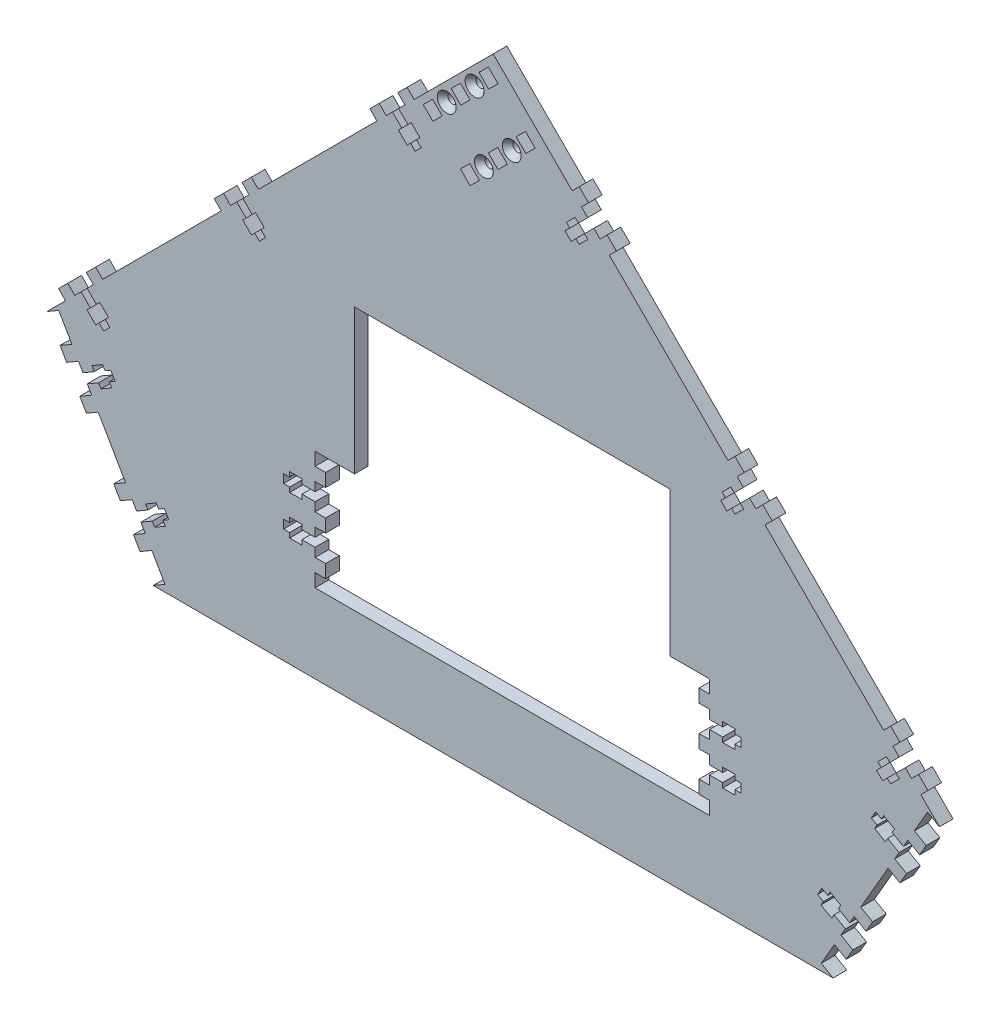
SolidWorks part; units mm, degrees
material "Acrylic (Blue)"
ref_plane "Front Plane" through (0, 0, 0) normal (0, 0, 1) x (1, 0, 0)
ref_plane "Top Plane" through (0, 0, 0) normal (0, 1, 0) x (1, 0, 0)
ref_plane "Right Plane" through (0, 0, 0) normal (1, 0, 0) x (0, 0, -1)
sketch "Sketch1" plane through (0, 0, 0) normal (0, 0, 1) x (1, 0, 0)
  line L0 (0, 0) -> (0, 304.4261) construction
  line L1 (0, 304.4261) -> (215.5261, 88.9)
  line L2 (215.5261, 88.9) -> (164.1997, 0)
  line L3 (164.1997, 0) -> (0, 0)
  line L4 (0, 304.4261) -> (-215.5261, 88.9)
  line L5 (-215.5261, 88.9) -> (-164.1997, 0)
  line L6 (-164.1997, 0) -> (0, 0)
  line L7 (-215.5261, 88.9) -> (215.5261, 88.9) construction
  line L8 (0, 304.4261) -> (3.5921, 308.0182) construction
  line L9 (3.5921, 308.0182) -> (219.1182, 92.4921) construction
  line L10 (219.1182, 92.4921) -> (215.5261, 88.9) construction
  line L11 (3.5921, 308.0182) -> (0, 311.6104) construction
  line L12 (0, 311.6104) -> (-219.1182, 92.4921) construction
  line L13 (-219.1182, 92.4921) -> (-215.5261, 88.9) construction
  line L14 (215.5261, 88.9) -> (219.9256, 86.36) construction
  line L15 (219.9256, 86.36) -> (168.5991, -2.54) construction
  line L16 (168.5991, -2.54) -> (164.1997, 0) construction
  line L17 (164.1997, 0) -> (164.1997, -12.7) construction
  line L18 (164.1997, -12.7) -> (-164.1997, -12.7) construction
  line L19 (-164.1997, -12.7) -> (-164.1997, 0) construction
  line L20 (-164.1997, 0) -> (-168.5991, -2.54) construction
  line L21 (-168.5991, -2.54) -> (-219.9256, 86.36) construction
  line L22 (-219.9256, 86.36) -> (-215.5261, 88.9) construction
  dimension "D1" = 304.8
  dimension "D2" = 120
  dimension "D3" = 88.9
  dimension "D4" = 5.08
  dimension "D5" = 12.7
extrude "Boss-Extrude1" add sketch "Sketch1" along normal blind 6.604
sketch "Sketch2" plane through (0, 0, 6.604) normal (0, 0, 1) x (1, 0, 0)
  line L0 (215.5261, 88.9) -> (0, 304.4261) construction
  line L1 (-66.9554, 165.1) -> (85.4446, 165.1)
  line L2 (-66.9554, 38.1) -> (85.4446, 38.1)
  line L3 (85.4446, 165.1) -> (85.4446, 95.25)
  line L4 (-66.9554, 165.1) -> (-66.9554, 95.25)
  line L6 (-164.1997, 0) -> (164.1997, 0) construction
  line L7 (-66.9554, 38.1) -> (-86.0054, 38.1)
  line L9 (-66.9554, 95.25) -> (-86.0054, 95.25)
  line L10 (-86.0054, 38.1) -> (-86.0054, 95.25)
  line L11 (85.4446, 38.1) -> (104.4946, 38.1)
  line L13 (85.4446, 95.25) -> (104.4946, 95.25)
  line L14 (104.4946, 38.1) -> (104.4946, 95.25)
  dimension "D1" = 127
  dimension "D2" = 38.1
  dimension "D3" = 38.1
  dimension "D4" = 152.4
  dimension "D5" = 19.05
  dimension "D6" = 57.15
extrude "Cut-Extrude1" cut sketch "Sketch2" against normal through all
sketch "Sketch3" plane through (0, 0, 6.604) normal (0, 0, 1) x (1, 0, 0)
  line L0 (-209.8069, 92.202) -> (-215.5261, 88.9)
  line L1 (-215.5261, 88.9) -> (-164.1997, 0)
  line L2 (-164.1997, 0) -> (-158.4805, 3.302)
  line L3 (-158.4805, 3.302) -> (-209.8069, 92.202)
  line L4 (0, 304.4261) -> (0, 0) construction
  line L5 (158.4805, 3.302) -> (209.8069, 92.202)
  line L6 (164.1997, 0) -> (158.4805, 3.302)
  line L7 (215.5261, 88.9) -> (164.1997, 0)
  line L8 (209.8069, 92.202) -> (215.5261, 88.9)
  dimension "D1" = 6.604
extrude "Cut-Extrude2" cut sketch "Sketch3" against normal through all
sketch "Sketch8" plane through (0, 0, 6.604) normal (0, 0, 1) x (1, 0, 0)
  line L0 (0, 304.4261) -> (-215.5261, 88.9) construction
  line L1 (215.5261, 88.9) -> (0, 304.4261) construction
  line B0 (-20.2954, 279.8202) -> (-15.8053, 284.3104)
  line B1 (-15.8053, 284.3104) -> (-11.1355, 279.6406)
  line B2 (-11.1355, 279.6406) -> (-15.6256, 275.1505)
  line B3 (-15.6256, 275.1505) -> (-20.2954, 279.8202)
  line B4 (-33.7658, 266.3499) -> (-29.2756, 270.84)
  line B5 (-29.2756, 270.84) -> (-24.6059, 266.1703)
  line B6 (-24.6059, 266.1703) -> (-29.096, 261.6801)
  line B7 (-29.096, 261.6801) -> (-33.7658, 266.3499)
  circle B8 centre (-22.4506, 272.9953) radius 2.1526
  line B9 (-6.825, 293.2906) -> (-2.3349, 297.7808)
  line B10 (-2.3349, 297.7808) -> (2.3349, 293.111)
  line B11 (-2.1553, 288.6209) -> (2.3349, 293.111)
  line B12 (-6.825, 293.2906) -> (-2.1553, 288.6209)
  circle B13 centre (-8.9803, 286.4656) radius 2.1527
  line B14 (-2.3349, 261.8597) -> (2.1553, 266.3499)
  line B15 (2.1553, 266.3499) -> (6.825, 261.6801)
  line B16 (6.825, 261.6801) -> (2.3349, 257.19)
  line B17 (2.3349, 257.19) -> (-2.3349, 261.8597)
  line B18 (-15.8053, 248.3893) -> (-11.3151, 252.8795)
  line B19 (-11.3151, 252.8795) -> (-6.6454, 248.2097)
  line B20 (-6.6454, 248.2097) -> (-11.1355, 243.7196)
  line B21 (-11.1355, 243.7196) -> (-15.8053, 248.3893)
  circle B22 centre (-4.4901, 255.0347) radius 2.1526
  line B23 (11.1355, 275.3301) -> (15.6256, 279.8202)
  line B24 (15.6256, 279.8202) -> (20.2954, 275.1505)
  line B25 (15.8053, 270.6604) -> (20.2954, 275.1505)
  line B26 (11.1355, 275.3301) -> (15.8053, 270.6604)
  circle B27 centre (8.9803, 268.5051) radius 2.1527
  dimension "D1" = 6.35
  dimension "D2" = 25.4
  dimension "D3" = 6.35
sketch_block_instance "BOLT_HOLE_2X-1"
sketch_block "BOLT_HOLE_2X" parameters "D1"=4.3053, "D2"=6.35, "D3"=6.35, "D4"=6.604
sketch_block_instance "BOLT_HOLE_2X-2"
extrude "Cut-Extrude4" cut sketch "Sketch8" against normal through all
sketch "Sketch4" plane through (0, 0, 6.604) normal (0, 0, 1) x (1, 0, 0)
  line L0 (0, 304.4261) -> (-215.5261, 88.9) construction
  line L1 (-59.5391, 251.712) -> (-116.7882, 194.4629) construction
  line L3 (-134.7487, 176.5024) -> (-191.9979, 119.2533) construction
  line L4 (215.5261, 88.9) -> (0, 304.4261) construction
  line L5 (134.7487, 176.5024) -> (191.9979, 119.2533) construction
  line L6 (59.5391, 251.712) -> (116.7882, 194.4629) construction
  line L7 (215.5261, 88.9) -> (209.8069, 92.202) construction
  line L8 (-158.4805, 3.302) -> (-209.8069, 92.202) construction
  line L9 (-209.8069, 92.202) -> (-215.5261, 88.9) construction
  line L11 (158.4805, 3.302) -> (164.1997, 0) construction
  line L13 (-164.1997, 0) -> (-158.4805, 3.302) construction
  line L14 (209.8069, 92.202) -> (158.4805, 3.302) construction
  line L15 (104.4946, 38.1) -> (104.4946, 95.25) construction
  line L16 (104.4946, 95.25) -> (85.4446, 95.25) construction
  line L17 (-86.0054, 95.25) -> (-86.0054, 38.1) construction
  line B0 (-48.6191, 255.807) -> (-44.129, 251.3169) construction
  line B1 (-44.129, 251.3169) -> (-45.7454, 249.7005) construction
  line B2 (-45.7454, 249.7005) -> (-41.5427, 245.4977) construction
  line B3 (-41.5427, 245.4977) -> (-39.9262, 247.1142) construction
  line B4 (-39.9262, 247.1142) -> (-37.6632, 244.8511) construction
  line B5 (-37.6632, 244.8511) -> (-34.7177, 247.7967) construction
  line B6 (-34.7177, 247.7967) -> (-36.9807, 250.0597) construction
  line B7 (-36.9807, 250.0597) -> (-35.3642, 251.6761) construction
  line B8 (-35.3642, 251.6761) -> (-39.567, 255.8789) construction
  line B9 (-39.567, 255.8789) -> (-41.1835, 254.2624) construction
  line B10 (-41.1835, 254.2624) -> (-45.6736, 258.7526) construction
  line B11 (-42.6562, 261.7699) -> (-46.0687, 265.1824) construction
  line B12 (-46.0687, 265.1824) -> (-41.5786, 269.6726) construction
  line B13 (-41.5786, 269.6726) -> (-38.1661, 266.2601) construction
  line B14 (-48.6191, 255.807) -> (-51.6365, 252.7897) construction
  line B15 (-51.6365, 252.7897) -> (-55.049, 256.2022) construction
  line B16 (-55.049, 256.2022) -> (-59.5391, 251.712) construction
  line B17 (-59.5391, 251.712) -> (-56.1266, 248.2995) construction
  line B18 (-45.6736, 258.7526) -> (-48.6191, 255.807) construction
  line B19 (-123.8288, 180.5974) -> (-119.3386, 176.1073) construction
  line B20 (-119.3386, 176.1073) -> (-120.9551, 174.4908) construction
  line B21 (-120.9551, 174.4908) -> (-116.7523, 170.2881) construction
  line B22 (-116.7523, 170.2881) -> (-115.1359, 171.9045) construction
  line B23 (-115.1359, 171.9045) -> (-112.8728, 169.6415) construction
  line B24 (-112.8728, 169.6415) -> (-109.9273, 172.587) construction
  line B25 (-109.9273, 172.587) -> (-112.1903, 174.85) construction
  line B26 (-112.1903, 174.85) -> (-110.5739, 176.4665) construction
  line B27 (-110.5739, 176.4665) -> (-114.7767, 180.6692) construction
  line B28 (-114.7767, 180.6692) -> (-116.3931, 179.0528) construction
  line B29 (-116.3931, 179.0528) -> (-120.8832, 183.5429) construction
  line B30 (-117.8659, 186.5603) -> (-121.2784, 189.9728) construction
  line B31 (-121.2784, 189.9728) -> (-116.7882, 194.4629) construction
  line B32 (-116.7882, 194.4629) -> (-113.3757, 191.0504) construction
  line B33 (-126.8461, 177.58) -> (-130.2586, 180.9925) construction
  line B34 (-130.2586, 180.9925) -> (-134.7487, 176.5024) construction
  line B35 (-134.7487, 176.5024) -> (-131.3362, 173.0899) construction
  line B36 (-120.8832, 183.5429) -> (-123.8288, 180.5974) construction
  line B37 (-199.0384, 105.3878) -> (-194.5483, 100.8976) construction
  line B38 (-194.5483, 100.8976) -> (-196.1647, 99.2812) construction
  line B39 (-196.1647, 99.2812) -> (-191.962, 95.0784) construction
  line B40 (-191.962, 95.0784) -> (-190.3455, 96.6949) construction
  line B41 (-190.3455, 96.6949) -> (-188.0825, 94.4318) construction
  line B42 (-188.0825, 94.4318) -> (-185.137, 97.3774) construction
  line B43 (-185.137, 97.3774) -> (-187.4, 99.6404) construction
  line B44 (-187.4, 99.6404) -> (-185.7835, 101.2568) construction
  line B45 (-185.7835, 101.2568) -> (-189.9863, 105.4596) construction
  line B46 (-189.9863, 105.4596) -> (-191.6027, 103.8431) construction
  line B47 (-191.6027, 103.8431) -> (-196.0929, 108.3333) construction
  line B48 (-196.0929, 108.3333) -> (-193.0755, 111.3506) construction
  line B49 (-193.0755, 111.3506) -> (-196.488, 114.7631) construction
  line B50 (-196.488, 114.7631) -> (-191.9979, 119.2533) construction
  line B51 (-191.9979, 119.2533) -> (-188.5854, 115.8408) construction
  line B52 (-199.0384, 105.3878) -> (-202.0558, 102.3704) construction
  line B53 (-202.0558, 102.3704) -> (-205.4683, 105.7829) construction
  line B54 (-205.4683, 105.7829) -> (-209.9584, 101.2928) construction
  line B55 (-209.9584, 101.2928) -> (-206.5459, 97.8803) construction
  line B56 (-196.0929, 108.3333) -> (-199.0384, 105.3878) construction
  line B57 (45.6736, 258.7526) -> (41.1835, 254.2624) construction
  line B58 (41.1835, 254.2624) -> (39.567, 255.8789) construction
  line B59 (39.567, 255.8789) -> (35.3642, 251.6761) construction
  line B60 (35.3642, 251.6761) -> (36.9807, 250.0597) construction
  line B61 (36.9807, 250.0597) -> (34.7177, 247.7967) construction
  line B62 (34.7177, 247.7967) -> (37.6632, 244.8511) construction
  line B63 (37.6632, 244.8511) -> (39.9262, 247.1142) construction
  line B64 (39.9262, 247.1142) -> (41.5427, 245.4977) construction
  line B65 (41.5427, 245.4977) -> (45.7454, 249.7005) construction
  line B66 (45.7454, 249.7005) -> (44.129, 251.3169) construction
  line B67 (44.129, 251.3169) -> (48.6191, 255.807) construction
  line B68 (48.6191, 255.807) -> (51.6365, 252.7897) construction
  line B69 (51.6365, 252.7897) -> (55.049, 256.2022) construction
  line B70 (55.049, 256.2022) -> (59.5391, 251.712) construction
  line B71 (59.5391, 251.712) -> (56.1266, 248.2995) construction
  line B72 (45.6736, 258.7526) -> (42.6562, 261.7699) construction
  line B73 (42.6562, 261.7699) -> (46.0687, 265.1824) construction
  line B74 (46.0687, 265.1824) -> (41.5786, 269.6726) construction
  line B75 (41.5786, 269.6726) -> (38.1661, 266.2601) construction
  line B76 (48.6191, 255.807) -> (45.6736, 258.7526) construction
  line B77 (120.8832, 183.5429) -> (116.3931, 179.0528) construction
  line B78 (116.3931, 179.0528) -> (114.7767, 180.6692) construction
  line B79 (114.7767, 180.6692) -> (110.5739, 176.4665) construction
  line B80 (110.5739, 176.4665) -> (112.1903, 174.85) construction
  line B81 (112.1903, 174.85) -> (109.9273, 172.587) construction
  line B82 (109.9273, 172.587) -> (112.8728, 169.6415) construction
  line B83 (112.8728, 169.6415) -> (115.1359, 171.9045) construction
  line B84 (115.1359, 171.9045) -> (116.7523, 170.2881) construction
  line B85 (116.7523, 170.2881) -> (120.9551, 174.4908) construction
  line B86 (120.9551, 174.4908) -> (119.3386, 176.1073) construction
  line B87 (119.3386, 176.1073) -> (123.8288, 180.5974) construction
  line B88 (123.8288, 180.5974) -> (126.8461, 177.58) construction
  line B89 (126.8461, 177.58) -> (130.2586, 180.9925) construction
  line B90 (130.2586, 180.9925) -> (134.7487, 176.5024) construction
  line B91 (134.7487, 176.5024) -> (131.3362, 173.0899) construction
  line B92 (120.8832, 183.5429) -> (117.8659, 186.5603) construction
  line B93 (117.8659, 186.5603) -> (121.2784, 189.9728) construction
  line B94 (121.2784, 189.9728) -> (116.7882, 194.4629) construction
  line B95 (116.7882, 194.4629) -> (113.3757, 191.0504) construction
  line B96 (123.8288, 180.5974) -> (120.8832, 183.5429) construction
  line B97 (196.0929, 108.3333) -> (191.6027, 103.8431) construction
  line B98 (191.6027, 103.8431) -> (189.9863, 105.4596) construction
  line B99 (189.9863, 105.4596) -> (185.7835, 101.2568) construction
  line B100 (185.7835, 101.2568) -> (187.4, 99.6404) construction
  line B101 (187.4, 99.6404) -> (185.137, 97.3774) construction
  line B102 (185.137, 97.3774) -> (188.0825, 94.4318) construction
  line B103 (188.0825, 94.4318) -> (190.3455, 96.6949) construction
  line B104 (190.3455, 96.6949) -> (191.962, 95.0784) construction
  line B105 (191.962, 95.0784) -> (196.1647, 99.2812) construction
  line B106 (196.1647, 99.2812) -> (194.5483, 100.8976) construction
  line B107 (194.5483, 100.8976) -> (199.0384, 105.3878) construction
  line B108 (199.0384, 105.3878) -> (202.0558, 102.3704) construction
  line B109 (202.0558, 102.3704) -> (205.4683, 105.7829) construction
  line B110 (205.4683, 105.7829) -> (209.9584, 101.2928) construction
  line B111 (209.9584, 101.2928) -> (206.5459, 97.8803) construction
  line B112 (193.0755, 111.3506) -> (196.488, 114.7631) construction
  line B113 (196.488, 114.7631) -> (191.9979, 119.2533) construction
  line B114 (191.9979, 119.2533) -> (188.5854, 115.8408) construction
  line B115 (199.0384, 105.3878) -> (196.0929, 108.3333) construction
  line B116 (198.1483, 72.0087) -> (192.6491, 75.1837) construction
  line B117 (192.6491, 75.1837) -> (193.7921, 77.1634) construction
  line B118 (193.7921, 77.1634) -> (188.6447, 80.1352) construction
  line B119 (188.6447, 80.1352) -> (187.5017, 78.1555) construction
  line B120 (187.5017, 78.1555) -> (184.7301, 79.7557) construction
  line B121 (184.7301, 79.7557) -> (182.6473, 76.1482) construction
  line B122 (182.6473, 76.1482) -> (185.4189, 74.548) construction
  line B123 (185.4189, 74.548) -> (184.2759, 72.5683) construction
  line B124 (184.2759, 72.5683) -> (189.4233, 69.5965) construction
  line B125 (189.4233, 69.5965) -> (190.5663, 71.5762) construction
  line B126 (190.5663, 71.5762) -> (196.0655, 68.4012) construction
  line B127 (196.0655, 68.4012) -> (193.9319, 64.7057) construction
  line B128 (193.9319, 64.7057) -> (198.1114, 62.2927) construction
  line B129 (198.1114, 62.2927) -> (194.9364, 56.7934) construction
  line B130 (194.9364, 56.7934) -> (190.7569, 59.2064) construction
  line B131 (198.1483, 72.0087) -> (200.2819, 75.7042) construction
  line B132 (200.2819, 75.7042) -> (204.4614, 73.2912) construction
  line B133 (204.4614, 73.2912) -> (207.6364, 78.7905) construction
  line B134 (207.6364, 78.7905) -> (203.4569, 81.2035) construction
  line B135 (196.0655, 68.4012) -> (198.1483, 72.0087) construction
  line B136 (172.2219, 27.1028) -> (166.7226, 30.2778) construction
  line B137 (166.7226, 30.2778) -> (167.8656, 32.2575) construction
  line B138 (167.8656, 32.2575) -> (162.7183, 35.2293) construction
  line B139 (162.7183, 35.2293) -> (161.5753, 33.2496) construction
  line B140 (161.5753, 33.2496) -> (158.8037, 34.8498) construction
  line B141 (158.8037, 34.8498) -> (156.7209, 31.2423) construction
  line B142 (156.7209, 31.2423) -> (159.4925, 29.6421) construction
  line B143 (159.4925, 29.6421) -> (158.3495, 27.6624) construction
  line B144 (158.3495, 27.6624) -> (163.4968, 24.6906) construction
  line B145 (163.4968, 24.6906) -> (164.6398, 26.6703) construction
  line B146 (164.6398, 26.6703) -> (170.1391, 23.4953) construction
  line B147 (170.1391, 23.4953) -> (168.0055, 19.7998) construction
  line B148 (168.0055, 19.7998) -> (172.1849, 17.3868) construction
  line B149 (172.1849, 17.3868) -> (169.0099, 11.8875) construction
  line B150 (169.0099, 11.8875) -> (164.8305, 14.3005) construction
  line B151 (172.2219, 27.1028) -> (174.3555, 30.7983) construction
  line B152 (174.3555, 30.7983) -> (178.5349, 28.3853) construction
  line B153 (178.5349, 28.3853) -> (181.7099, 33.8846) construction
  line B154 (181.7099, 33.8846) -> (177.5305, 36.2976) construction
  line B155 (170.1391, 23.4953) -> (172.2219, 27.1028) construction
  line B156 (-170.1391, 23.4953) -> (-164.6398, 26.6703) construction
  line B157 (-164.6398, 26.6703) -> (-163.4968, 24.6906) construction
  line B158 (-163.4968, 24.6906) -> (-158.3495, 27.6624) construction
  line B159 (-158.3495, 27.6624) -> (-159.4925, 29.6421) construction
  line B160 (-159.4925, 29.6421) -> (-156.7209, 31.2423) construction
  line B161 (-156.7209, 31.2423) -> (-158.8037, 34.8498) construction
  line B162 (-158.8037, 34.8498) -> (-161.5753, 33.2496) construction
  line B163 (-161.5753, 33.2496) -> (-162.7183, 35.2293) construction
  line B164 (-162.7183, 35.2293) -> (-167.8656, 32.2575) construction
  line B165 (-167.8656, 32.2575) -> (-166.7226, 30.2778) construction
  line B166 (-166.7226, 30.2778) -> (-172.2219, 27.1028) construction
  line B167 (-172.2219, 27.1028) -> (-174.3555, 30.7983) construction
  line B168 (-174.3555, 30.7983) -> (-178.5349, 28.3853) construction
  line B169 (-178.5349, 28.3853) -> (-181.7099, 33.8846) construction
  line B170 (-181.7099, 33.8846) -> (-177.5305, 36.2976) construction
  line B171 (-168.0055, 19.7998) -> (-172.1849, 17.3868) construction
  line B172 (-172.1849, 17.3868) -> (-169.0099, 11.8875) construction
  line B173 (-169.0099, 11.8875) -> (-164.8305, 14.3005) construction
  line B174 (-172.2219, 27.1028) -> (-170.1391, 23.4953) construction
  line B175 (-196.0655, 68.4012) -> (-190.5663, 71.5762) construction
  line B176 (-190.5663, 71.5762) -> (-189.4233, 69.5965) construction
  line B177 (-189.4233, 69.5965) -> (-184.2759, 72.5683) construction
  line B178 (-184.2759, 72.5683) -> (-185.4189, 74.548) construction
  line B179 (-185.4189, 74.548) -> (-182.6473, 76.1482) construction
  line B180 (-182.6473, 76.1482) -> (-184.7301, 79.7557) construction
  line B181 (-184.7301, 79.7557) -> (-187.5017, 78.1555) construction
  line B182 (-187.5017, 78.1555) -> (-188.6447, 80.1352) construction
  line B183 (-188.6447, 80.1352) -> (-193.7921, 77.1634) construction
  line B184 (-193.7921, 77.1634) -> (-192.6491, 75.1837) construction
  line B185 (-192.6491, 75.1837) -> (-198.1483, 72.0087) construction
  line B186 (-200.2819, 75.7042) -> (-204.4614, 73.2912) construction
  line B187 (-204.4614, 73.2912) -> (-207.6364, 78.7905) construction
  line B188 (-207.6364, 78.7905) -> (-203.4569, 81.2035) construction
  line B189 (-196.0655, 68.4012) -> (-193.9319, 64.7057) construction
  line B190 (-193.9319, 64.7057) -> (-198.1114, 62.2927) construction
  line B191 (-198.1114, 62.2927) -> (-194.9364, 56.7934) construction
  line B192 (-194.9364, 56.7934) -> (-190.7569, 59.2064) construction
  line B193 (-198.1483, 72.0087) -> (-196.0655, 68.4012) construction
  line B194 (-86.0054, 78.2828) -> (-92.3554, 78.2828)
  line B195 (-92.3554, 78.2828) -> (-92.3554, 80.5688)
  line B196 (-92.3554, 80.5688) -> (-98.299, 80.5688)
  line B197 (-98.299, 80.5688) -> (-98.299, 78.2828)
  line B198 (-98.299, 78.2828) -> (-101.2454, 78.2828)
  line B199 (-101.2454, 78.2828) -> (-101.2454, 74.1172)
  line B200 (-101.2454, 74.1172) -> (-98.299, 74.1172)
  line B201 (-98.299, 74.1172) -> (-98.299, 71.8312)
  line B202 (-98.299, 71.8312) -> (-92.3554, 71.8312)
  line B203 (-92.3554, 71.8312) -> (-92.3554, 74.1172)
  line B204 (-92.3554, 74.1172) -> (-86.0054, 74.1172)
  line B205 (-86.0054, 69.85) -> (-80.9254, 69.85)
  line B206 (-80.9254, 69.85) -> (-80.9254, 63.5)
  line B207 (-80.9254, 63.5) -> (-86.0054, 63.5)
  line B208 (-86.0054, 78.2828) -> (-86.0054, 82.55)
  line B209 (-86.0054, 82.55) -> (-80.9254, 82.55)
  line B210 (-80.9254, 82.55) -> (-80.9254, 88.9)
  line B211 (-80.9254, 88.9) -> (-86.0054, 88.9)
  line B212 (-86.0054, 74.1172) -> (-86.0054, 78.2828) construction
  line B213 (-80.9254, 44.45) -> (-86.0054, 44.45)
  line B214 (-86.0054, 59.2328) -> (-92.3554, 59.2328)
  line B215 (-92.3554, 59.2328) -> (-92.3554, 61.5188)
  line B216 (-92.3554, 61.5188) -> (-98.299, 61.5188)
  line B217 (-98.299, 61.5188) -> (-98.299, 59.2328)
  line B218 (-98.299, 59.2328) -> (-101.2454, 59.2328)
  line B219 (-101.2454, 59.2328) -> (-101.2454, 55.0672)
  line B220 (-101.2454, 55.0672) -> (-98.299, 55.0672)
  line B221 (-98.299, 55.0672) -> (-98.299, 52.7812)
  line B222 (-98.299, 52.7812) -> (-92.3554, 52.7812)
  line B223 (-92.3554, 52.7812) -> (-92.3554, 55.0672)
  line B224 (-92.3554, 55.0672) -> (-86.0054, 55.0672)
  line B225 (-86.0054, 55.0672) -> (-86.0054, 50.8)
  line B226 (-86.0054, 50.8) -> (-80.9254, 50.8)
  line B227 (-80.9254, 50.8) -> (-80.9254, 44.45)
  line B228 (-86.0054, 59.2328) -> (-86.0054, 63.5)
  line B229 (-86.0054, 55.0672) -> (-86.0054, 59.2328) construction
  line B230 (104.4946, 55.0672) -> (110.8446, 55.0672)
  line B231 (110.8446, 55.0672) -> (110.8446, 52.7812)
  line B232 (110.8446, 52.7812) -> (116.7882, 52.7812)
  line B233 (116.7882, 52.7812) -> (116.7882, 55.0672)
  line B234 (116.7882, 55.0672) -> (119.7346, 55.0672)
  line B235 (119.7346, 55.0672) -> (119.7346, 59.2328)
  line B236 (119.7346, 59.2328) -> (116.7882, 59.2328)
  line B237 (116.7882, 59.2328) -> (116.7882, 61.5188)
  line B238 (116.7882, 61.5188) -> (110.8446, 61.5188)
  line B239 (110.8446, 61.5188) -> (110.8446, 59.2328)
  line B240 (110.8446, 59.2328) -> (104.4946, 59.2328)
  line B241 (104.4946, 59.2328) -> (104.4946, 63.5)
  line B242 (104.4946, 63.5) -> (99.4146, 63.5)
  line B243 (99.4146, 63.5) -> (99.4146, 69.85)
  line B244 (99.4146, 69.85) -> (104.4946, 69.85)
  line B245 (104.4946, 55.0672) -> (104.4946, 50.8)
  line B246 (104.4946, 50.8) -> (99.4146, 50.8)
  line B247 (99.4146, 50.8) -> (99.4146, 44.45)
  line B248 (99.4146, 44.45) -> (104.4946, 44.45)
  line B249 (104.4946, 59.2328) -> (104.4946, 55.0672) construction
  line B250 (99.4146, 88.9) -> (104.4946, 88.9)
  line B251 (104.4946, 74.1172) -> (110.8446, 74.1172)
  line B252 (110.8446, 74.1172) -> (110.8446, 71.8312)
  line B253 (110.8446, 71.8312) -> (116.7882, 71.8312)
  line B254 (116.7882, 71.8312) -> (116.7882, 74.1172)
  line B255 (116.7882, 74.1172) -> (119.7346, 74.1172)
  line B256 (119.7346, 74.1172) -> (119.7346, 78.2828)
  line B257 (119.7346, 78.2828) -> (116.7882, 78.2828)
  line B258 (116.7882, 78.2828) -> (116.7882, 80.5688)
  line B259 (116.7882, 80.5688) -> (110.8446, 80.5688)
  line B260 (110.8446, 80.5688) -> (110.8446, 78.2828)
  line B261 (110.8446, 78.2828) -> (104.4946, 78.2828)
  line B262 (104.4946, 78.2828) -> (104.4946, 82.55)
  line B263 (104.4946, 82.55) -> (99.4146, 82.55)
  line B264 (99.4146, 82.55) -> (99.4146, 88.9)
  line B265 (104.4946, 78.2828) -> (104.4946, 74.1172) construction
  dimension "D1" = 12.7
  dimension "D2" = 53.975
  dimension "D3" = 53.975
  dimension "D4" = 12.7
  dimension "D5" = 12.7
  dimension "D6" = 12.7
  dimension "D7" = 12.7
  dimension "D8" = 12.7
  dimension "D9" = 6.35
sketch_block_instance "NUT_HOLE-1"
sketch_block "NUT_HOLE" parameters "D1"=6.35, "D2"=4.1656, "D3"=25.4, "D4"=4.826, "D5"=8.7376, "D6"=5.9436, "D7"=6.35, "D8"=20.32
sketch_block_instance "NUT_HOLE-2"
sketch_block_instance "NUT_HOLE-3"
sketch_block_instance "NUT_HOLE-4"
sketch_block_instance "NUT_HOLE-5"
sketch_block_instance "NUT_HOLE-6"
sketch_block_instance "NUT_HOLE-7"
sketch_block_instance "NUT_HOLE-8"
sketch_block_instance "NUT_HOLE-9"
sketch_block_instance "NUT_HOLE-10"
sketch_block_instance "NUT_HOLE_2X-1"
sketch_block "NUT_HOLE_2X" parameters "D1"=6.35, "D2"=4.1656, "D3"=25.4, "D4"=5.08, "D5"=8.7376, "D6"=5.9436, "D7"=6.35, "D8"=20.32, "D9"=2
sketch_block_instance "NUT_HOLE_2X-2"
sketch "Sketch6" plane through (0, 0, 6.604) normal (0, 0, 1) x (1, 0, 0)
  line L0 (-41.1835, 254.2624) -> (-45.6736, 258.7526) construction
  line L1 (-39.567, 255.8789) -> (-41.1835, 254.2624) construction
  line L2 (-35.3642, 251.6761) -> (-39.567, 255.8789) construction
  line L3 (-48.6191, 255.807) -> (-44.129, 251.3169) construction
  line L4 (-44.129, 251.3169) -> (-45.7454, 249.7005) construction
  line L5 (-45.7454, 249.7005) -> (-41.5427, 245.4977) construction
  line L6 (-41.5427, 245.4977) -> (-39.9262, 247.1142) construction
  line L7 (-39.9262, 247.1142) -> (-37.6632, 244.8511) construction
  line L8 (-34.7177, 247.7967) -> (-36.9807, 250.0597) construction
  line L9 (-36.9807, 250.0597) -> (-35.3642, 251.6761) construction
  line L10 (-37.6632, 244.8511) -> (-34.7177, 247.7967) construction
  line L11 (-116.3931, 179.0528) -> (-120.8832, 183.5429) construction
  line L12 (-114.7767, 180.6692) -> (-116.3931, 179.0528) construction
  line L13 (-110.5739, 176.4665) -> (-114.7767, 180.6692) construction
  line L14 (-112.1903, 174.85) -> (-110.5739, 176.4665) construction
  line L15 (-109.9273, 172.587) -> (-112.1903, 174.85) construction
  line L16 (-112.8728, 169.6415) -> (-109.9273, 172.587) construction
  line L17 (-115.1359, 171.9045) -> (-112.8728, 169.6415) construction
  line L18 (-116.7523, 170.2881) -> (-115.1359, 171.9045) construction
  line L19 (-120.9551, 174.4908) -> (-116.7523, 170.2881) construction
  line L20 (-119.3386, 176.1073) -> (-120.9551, 174.4908) construction
  line L21 (-123.8288, 180.5974) -> (-119.3386, 176.1073) construction
  line L22 (-199.0384, 105.3878) -> (-194.5483, 100.8976) construction
  line L23 (-191.6027, 103.8431) -> (-196.0929, 108.3333) construction
  line L24 (-194.5483, 100.8976) -> (-196.1647, 99.2812) construction
  line L25 (-196.1647, 99.2812) -> (-191.962, 95.0784) construction
  line L26 (-191.962, 95.0784) -> (-190.3455, 96.6949) construction
  line L27 (-190.3455, 96.6949) -> (-188.0825, 94.4318) construction
  line L28 (-188.0825, 94.4318) -> (-185.137, 97.3774) construction
  line L29 (-185.137, 97.3774) -> (-187.4, 99.6404) construction
  line L30 (-187.4, 99.6404) -> (-185.7835, 101.2568) construction
  line L31 (-189.9863, 105.4596) -> (-191.6027, 103.8431) construction
  line L32 (-185.7835, 101.2568) -> (-189.9863, 105.4596) construction
  line L33 (-192.6491, 75.1837) -> (-198.1483, 72.0087) construction
  line L34 (-193.7921, 77.1634) -> (-192.6491, 75.1837) construction
  line L35 (-188.6447, 80.1352) -> (-193.7921, 77.1634) construction
  line L36 (-187.5017, 78.1555) -> (-188.6447, 80.1352) construction
  line L37 (-184.7301, 79.7557) -> (-187.5017, 78.1555) construction
  line L38 (-182.6473, 76.1482) -> (-184.7301, 79.7557) construction
  line L39 (-185.4189, 74.548) -> (-182.6473, 76.1482) construction
  line L40 (-189.4233, 69.5965) -> (-184.2759, 72.5683) construction
  line L41 (-184.2759, 72.5683) -> (-185.4189, 74.548) construction
  line L42 (-196.0655, 68.4012) -> (-190.5663, 71.5762) construction
  line L43 (-190.5663, 71.5762) -> (-189.4233, 69.5965) construction
  line L44 (-166.7226, 30.2778) -> (-172.2219, 27.1028) construction
  line L45 (-167.8656, 32.2575) -> (-166.7226, 30.2778) construction
  line L46 (-162.7183, 35.2293) -> (-167.8656, 32.2575) construction
  line L47 (-161.5753, 33.2496) -> (-162.7183, 35.2293) construction
  line L48 (-158.8037, 34.8498) -> (-161.5753, 33.2496) construction
  line L49 (-156.7209, 31.2423) -> (-158.8037, 34.8498) construction
  line L50 (-159.4925, 29.6421) -> (-156.7209, 31.2423) construction
  line L51 (-158.3495, 27.6624) -> (-159.4925, 29.6421) construction
  line L52 (-163.4968, 24.6906) -> (-158.3495, 27.6624) construction
  line L53 (-164.6398, 26.6703) -> (-163.4968, 24.6906) construction
  line L54 (-170.1391, 23.4953) -> (-164.6398, 26.6703) construction
  line L55 (39.567, 255.8789) -> (35.3642, 251.6761) construction
  line L56 (41.1835, 254.2624) -> (39.567, 255.8789) construction
  line L57 (45.6736, 258.7526) -> (41.1835, 254.2624) construction
  line L58 (44.129, 251.3169) -> (48.6191, 255.807) construction
  line L59 (45.7454, 249.7005) -> (44.129, 251.3169) construction
  line L60 (41.5427, 245.4977) -> (45.7454, 249.7005) construction
  line L61 (39.9262, 247.1142) -> (41.5427, 245.4977) construction
  line L62 (37.6632, 244.8511) -> (39.9262, 247.1142) construction
  line L63 (34.7177, 247.7967) -> (37.6632, 244.8511) construction
  line L64 (36.9807, 250.0597) -> (34.7177, 247.7967) construction
  line L65 (35.3642, 251.6761) -> (36.9807, 250.0597) construction
  line L66 (120.8832, 183.5429) -> (116.3931, 179.0528) construction
  line L67 (116.3931, 179.0528) -> (114.7767, 180.6692) construction
  line L68 (114.7767, 180.6692) -> (110.5739, 176.4665) construction
  line L69 (110.5739, 176.4665) -> (112.1903, 174.85) construction
  line L70 (112.1903, 174.85) -> (109.9273, 172.587) construction
  line L71 (109.9273, 172.587) -> (112.8728, 169.6415) construction
  line L72 (112.8728, 169.6415) -> (115.1359, 171.9045) construction
  line L73 (115.1359, 171.9045) -> (116.7523, 170.2881) construction
  line L74 (116.7523, 170.2881) -> (120.9551, 174.4908) construction
  line L75 (119.3386, 176.1073) -> (123.8288, 180.5974) construction
  line L76 (120.9551, 174.4908) -> (119.3386, 176.1073) construction
  line L77 (194.5483, 100.8976) -> (199.0384, 105.3878) construction
  line L78 (196.0929, 108.3333) -> (191.6027, 103.8431) construction
  line L79 (189.9863, 105.4596) -> (185.7835, 101.2568) construction
  line L80 (191.6027, 103.8431) -> (189.9863, 105.4596) construction
  line L81 (185.7835, 101.2568) -> (187.4, 99.6404) construction
  line L82 (187.4, 99.6404) -> (185.137, 97.3774) construction
  line L83 (185.137, 97.3774) -> (188.0825, 94.4318) construction
  line L84 (188.0825, 94.4318) -> (190.3455, 96.6949) construction
  line L85 (190.3455, 96.6949) -> (191.962, 95.0784) construction
  line L86 (191.962, 95.0784) -> (196.1647, 99.2812) construction
  line L87 (196.1647, 99.2812) -> (194.5483, 100.8976) construction
  line L88 (188.6447, 80.1352) -> (187.5017, 78.1555) construction
  line L89 (187.5017, 78.1555) -> (184.7301, 79.7557) construction
  line L90 (184.7301, 79.7557) -> (182.6473, 76.1482) construction
  line L91 (182.6473, 76.1482) -> (185.4189, 74.548) construction
  line L92 (185.4189, 74.548) -> (184.2759, 72.5683) construction
  line L93 (184.2759, 72.5683) -> (189.4233, 69.5965) construction
  line L94 (193.7921, 77.1634) -> (188.6447, 80.1352) construction
  line L95 (192.6491, 75.1837) -> (193.7921, 77.1634) construction
  line L96 (198.1483, 72.0087) -> (192.6491, 75.1837) construction
  line L97 (190.5663, 71.5762) -> (196.0655, 68.4012) construction
  line L98 (189.4233, 69.5965) -> (190.5663, 71.5762) construction
  line L99 (161.5753, 33.2496) -> (158.8037, 34.8498) construction
  line L100 (158.8037, 34.8498) -> (156.7209, 31.2423) construction
  line L101 (162.7183, 35.2293) -> (161.5753, 33.2496) construction
  line L102 (167.8656, 32.2575) -> (162.7183, 35.2293) construction
  line L103 (166.7226, 30.2778) -> (167.8656, 32.2575) construction
  line L104 (172.2219, 27.1028) -> (166.7226, 30.2778) construction
  line L105 (164.6398, 26.6703) -> (170.1391, 23.4953) construction
  line L106 (163.4968, 24.6906) -> (164.6398, 26.6703) construction
  line L107 (156.7209, 31.2423) -> (159.4925, 29.6421) construction
  line L108 (159.4925, 29.6421) -> (158.3495, 27.6624) construction
  line L109 (158.3495, 27.6624) -> (163.4968, 24.6906) construction
  line L110 (-41.1835, 254.2624) -> (-45.6736, 258.7526)
  line L111 (-39.567, 255.8789) -> (-41.1835, 254.2624)
  line L112 (-35.3642, 251.6761) -> (-39.567, 255.8789)
  line L113 (-48.6191, 255.807) -> (-44.129, 251.3169)
  line L114 (-44.129, 251.3169) -> (-45.7454, 249.7005)
  line L115 (-45.7454, 249.7005) -> (-41.5427, 245.4977)
  line L116 (-41.5427, 245.4977) -> (-39.9262, 247.1142)
  line L117 (-39.9262, 247.1142) -> (-37.6632, 244.8511)
  line L118 (-34.7177, 247.7967) -> (-36.9807, 250.0597)
  line L119 (-36.9807, 250.0597) -> (-35.3642, 251.6761)
  line L120 (-37.6632, 244.8511) -> (-34.7177, 247.7967)
  line L121 (-116.3931, 179.0528) -> (-120.8832, 183.5429)
  line L122 (-114.7767, 180.6692) -> (-116.3931, 179.0528)
  line L123 (-110.5739, 176.4665) -> (-114.7767, 180.6692)
  line L124 (-112.1903, 174.85) -> (-110.5739, 176.4665)
  line L125 (-109.9273, 172.587) -> (-112.1903, 174.85)
  line L126 (-112.8728, 169.6415) -> (-109.9273, 172.587)
  line L127 (-115.1359, 171.9045) -> (-112.8728, 169.6415)
  line L128 (-116.7523, 170.2881) -> (-115.1359, 171.9045)
  line L129 (-120.9551, 174.4908) -> (-116.7523, 170.2881)
  line L130 (-119.3386, 176.1073) -> (-120.9551, 174.4908)
  line L131 (-123.8288, 180.5974) -> (-119.3386, 176.1073)
  line L132 (-199.0384, 105.3878) -> (-194.5483, 100.8976)
  line L133 (-191.6027, 103.8431) -> (-196.0929, 108.3333)
  line L134 (-194.5483, 100.8976) -> (-196.1647, 99.2812)
  line L135 (-196.1647, 99.2812) -> (-191.962, 95.0784)
  line L136 (-191.962, 95.0784) -> (-190.3455, 96.6949)
  line L137 (-190.3455, 96.6949) -> (-188.0825, 94.4318)
  line L138 (-188.0825, 94.4318) -> (-185.137, 97.3774)
  line L139 (-185.137, 97.3774) -> (-187.4, 99.6404)
  line L140 (-187.4, 99.6404) -> (-185.7835, 101.2568)
  line L141 (-189.9863, 105.4596) -> (-191.6027, 103.8431)
  line L142 (-185.7835, 101.2568) -> (-189.9863, 105.4596)
  line L143 (-192.6491, 75.1837) -> (-198.1483, 72.0087)
  line L144 (-193.7921, 77.1634) -> (-192.6491, 75.1837)
  line L145 (-188.6447, 80.1352) -> (-193.7921, 77.1634)
  line L146 (-187.5017, 78.1555) -> (-188.6447, 80.1352)
  line L147 (-184.7301, 79.7557) -> (-187.5017, 78.1555)
  line L148 (-182.6473, 76.1482) -> (-184.7301, 79.7557)
  line L149 (-185.4189, 74.548) -> (-182.6473, 76.1482)
  line L150 (-189.4233, 69.5965) -> (-184.2759, 72.5683)
  line L151 (-184.2759, 72.5683) -> (-185.4189, 74.548)
  line L152 (-196.0655, 68.4012) -> (-190.5663, 71.5762)
  line L153 (-190.5663, 71.5762) -> (-189.4233, 69.5965)
  line L154 (-166.7226, 30.2778) -> (-172.2219, 27.1028)
  line L155 (-167.8656, 32.2575) -> (-166.7226, 30.2778)
  line L156 (-162.7183, 35.2293) -> (-167.8656, 32.2575)
  line L157 (-161.5753, 33.2496) -> (-162.7183, 35.2293)
  line L158 (-158.8037, 34.8498) -> (-161.5753, 33.2496)
  line L159 (-156.7209, 31.2423) -> (-158.8037, 34.8498)
  line L160 (-159.4925, 29.6421) -> (-156.7209, 31.2423)
  line L161 (-158.3495, 27.6624) -> (-159.4925, 29.6421)
  line L162 (-163.4968, 24.6906) -> (-158.3495, 27.6624)
  line L163 (-164.6398, 26.6703) -> (-163.4968, 24.6906)
  line L164 (-170.1391, 23.4953) -> (-164.6398, 26.6703)
  line L165 (39.567, 255.8789) -> (35.3642, 251.6761)
  line L166 (41.1835, 254.2624) -> (39.567, 255.8789)
  line L167 (45.6736, 258.7526) -> (41.1835, 254.2624)
  line L168 (44.129, 251.3169) -> (48.6191, 255.807)
  line L169 (45.7454, 249.7005) -> (44.129, 251.3169)
  line L170 (41.5427, 245.4977) -> (45.7454, 249.7005)
  line L171 (39.9262, 247.1142) -> (41.5427, 245.4977)
  line L172 (37.6632, 244.8511) -> (39.9262, 247.1142)
  line L173 (34.7177, 247.7967) -> (37.6632, 244.8511)
  line L174 (36.9807, 250.0597) -> (34.7177, 247.7967)
  line L175 (35.3642, 251.6761) -> (36.9807, 250.0597)
  line L176 (120.8832, 183.5429) -> (116.3931, 179.0528)
  line L177 (116.3931, 179.0528) -> (114.7767, 180.6692)
  line L178 (114.7767, 180.6692) -> (110.5739, 176.4665)
  line L179 (110.5739, 176.4665) -> (112.1903, 174.85)
  line L180 (112.1903, 174.85) -> (109.9273, 172.587)
  line L181 (109.9273, 172.587) -> (112.8728, 169.6415)
  line L182 (112.8728, 169.6415) -> (115.1359, 171.9045)
  line L183 (115.1359, 171.9045) -> (116.7523, 170.2881)
  line L184 (116.7523, 170.2881) -> (120.9551, 174.4908)
  line L185 (119.3386, 176.1073) -> (123.8288, 180.5974)
  line L186 (120.9551, 174.4908) -> (119.3386, 176.1073)
  line L187 (194.5483, 100.8976) -> (199.0384, 105.3878)
  line L188 (196.0929, 108.3333) -> (191.6027, 103.8431)
  line L189 (189.9863, 105.4596) -> (185.7835, 101.2568)
  line L190 (191.6027, 103.8431) -> (189.9863, 105.4596)
  line L191 (185.7835, 101.2568) -> (187.4, 99.6404)
  line L192 (187.4, 99.6404) -> (185.137, 97.3774)
  line L193 (185.137, 97.3774) -> (188.0825, 94.4318)
  line L194 (188.0825, 94.4318) -> (190.3455, 96.6949)
  line L195 (190.3455, 96.6949) -> (191.962, 95.0784)
  line L196 (191.962, 95.0784) -> (196.1647, 99.2812)
  line L197 (196.1647, 99.2812) -> (194.5483, 100.8976)
  line L198 (188.6447, 80.1352) -> (187.5017, 78.1555)
  line L199 (187.5017, 78.1555) -> (184.7301, 79.7557)
  line L200 (184.7301, 79.7557) -> (182.6473, 76.1482)
  line L201 (182.6473, 76.1482) -> (185.4189, 74.548)
  line L202 (185.4189, 74.548) -> (184.2759, 72.5683)
  line L203 (184.2759, 72.5683) -> (189.4233, 69.5965)
  line L204 (193.7921, 77.1634) -> (188.6447, 80.1352)
  line L205 (192.6491, 75.1837) -> (193.7921, 77.1634)
  line L206 (198.1483, 72.0087) -> (192.6491, 75.1837)
  line L207 (190.5663, 71.5762) -> (196.0655, 68.4012)
  line L208 (189.4233, 69.5965) -> (190.5663, 71.5762)
  line L209 (161.5753, 33.2496) -> (158.8037, 34.8498)
  line L210 (158.8037, 34.8498) -> (156.7209, 31.2423)
  line L211 (162.7183, 35.2293) -> (161.5753, 33.2496)
  line L212 (167.8656, 32.2575) -> (162.7183, 35.2293)
  line L213 (166.7226, 30.2778) -> (167.8656, 32.2575)
  line L214 (172.2219, 27.1028) -> (166.7226, 30.2778)
  line L215 (164.6398, 26.6703) -> (170.1391, 23.4953)
  line L216 (163.4968, 24.6906) -> (164.6398, 26.6703)
  line L217 (156.7209, 31.2423) -> (159.4925, 29.6421)
  line L218 (159.4925, 29.6421) -> (158.3495, 27.6624)
  line L219 (158.3495, 27.6624) -> (163.4968, 24.6906)
  line L220 (-45.6736, 258.7526) -> (-48.6191, 255.807)
  line L221 (-120.8832, 183.5429) -> (-123.8288, 180.5974)
  line L222 (-196.0929, 108.3333) -> (-199.0384, 105.3878)
  line L223 (-198.1483, 72.0087) -> (-196.0655, 68.4012)
  line L224 (-170.1391, 23.4953) -> (-172.2219, 27.1028)
  line L226 (170.1391, 23.4953) -> (172.2219, 27.1028)
  line L227 (198.1483, 72.0087) -> (196.0655, 68.4012)
  line L228 (199.0384, 105.3878) -> (196.0929, 108.3333)
  line L229 (120.8832, 183.5429) -> (123.8288, 180.5974)
  line L230 (45.6736, 258.7526) -> (48.6191, 255.807)
  line L241 (-86.0054, 78.2828) -> (-92.3554, 78.2828) construction
  line L242 (-92.3554, 80.5688) -> (-98.299, 80.5688) construction
  line L243 (-98.299, 78.2828) -> (-101.2454, 78.2828) construction
  line L244 (-101.2454, 74.1172) -> (-98.299, 74.1172) construction
  line L245 (-98.299, 71.8312) -> (-92.3554, 71.8312) construction
  line L246 (-92.3554, 74.1172) -> (-86.0054, 74.1172) construction
  line L247 (-92.3554, 71.8312) -> (-92.3554, 74.1172) construction
  line L248 (-98.299, 74.1172) -> (-98.299, 71.8312) construction
  line L249 (-101.2454, 78.2828) -> (-101.2454, 74.1172) construction
  line L250 (-98.299, 80.5688) -> (-98.299, 78.2828) construction
  line L251 (-92.3554, 78.2828) -> (-92.3554, 80.5688) construction
  line L263 (-86.0054, 59.2328) -> (-92.3554, 59.2328) construction
  line L264 (-92.3554, 59.2328) -> (-92.3554, 61.5188) construction
  line L265 (-92.3554, 61.5188) -> (-98.299, 61.5188) construction
  line L266 (-98.299, 61.5188) -> (-98.299, 59.2328) construction
  line L267 (-98.299, 59.2328) -> (-101.2454, 59.2328) construction
  line L268 (-101.2454, 59.2328) -> (-101.2454, 55.0672) construction
  line L269 (-101.2454, 55.0672) -> (-98.299, 55.0672) construction
  line L270 (-98.299, 55.0672) -> (-98.299, 52.7812) construction
  line L271 (-98.299, 52.7812) -> (-92.3554, 52.7812) construction
  line L272 (-92.3554, 55.0672) -> (-86.0054, 55.0672) construction
  line L273 (-92.3554, 52.7812) -> (-92.3554, 55.0672) construction
  line L274 (110.8446, 78.2828) -> (104.4946, 78.2828) construction
  line L275 (110.8446, 80.5688) -> (110.8446, 78.2828) construction
  line L276 (116.7882, 80.5688) -> (110.8446, 80.5688) construction
  line L277 (116.7882, 78.2828) -> (116.7882, 80.5688) construction
  line L278 (119.7346, 78.2828) -> (116.7882, 78.2828) construction
  line L279 (119.7346, 74.1172) -> (119.7346, 78.2828) construction
  line L280 (116.7882, 74.1172) -> (119.7346, 74.1172) construction
  line L281 (116.7882, 71.8312) -> (116.7882, 74.1172) construction
  line L282 (110.8446, 71.8312) -> (116.7882, 71.8312) construction
  line L283 (110.8446, 74.1172) -> (110.8446, 71.8312) construction
  line L284 (104.4946, 74.1172) -> (110.8446, 74.1172) construction
  line L285 (116.7882, 61.5188) -> (110.8446, 61.5188) construction
  line L286 (110.8446, 61.5188) -> (110.8446, 59.2328) construction
  line L287 (116.7882, 59.2328) -> (116.7882, 61.5188) construction
  line L288 (119.7346, 59.2328) -> (116.7882, 59.2328) construction
  line L289 (119.7346, 55.0672) -> (119.7346, 59.2328) construction
  line L290 (116.7882, 55.0672) -> (119.7346, 55.0672) construction
  line L291 (116.7882, 52.7812) -> (116.7882, 55.0672) construction
  line L292 (110.8446, 52.7812) -> (116.7882, 52.7812) construction
  line L293 (104.4946, 55.0672) -> (110.8446, 55.0672) construction
  line L294 (110.8446, 55.0672) -> (110.8446, 52.7812) construction
  line L295 (110.8446, 59.2328) -> (104.4946, 59.2328) construction
  line L296 (-86.0054, 78.2828) -> (-92.3554, 78.2828)
  line L297 (-92.3554, 80.5688) -> (-98.299, 80.5688)
  line L298 (-98.299, 78.2828) -> (-101.2454, 78.2828)
  line L299 (-101.2454, 74.1172) -> (-98.299, 74.1172)
  line L300 (-98.299, 71.8312) -> (-92.3554, 71.8312)
  line L301 (-92.3554, 74.1172) -> (-86.0054, 74.1172)
  line L302 (-92.3554, 71.8312) -> (-92.3554, 74.1172)
  line L303 (-98.299, 74.1172) -> (-98.299, 71.8312)
  line L304 (-101.2454, 78.2828) -> (-101.2454, 74.1172)
  line L305 (-98.299, 80.5688) -> (-98.299, 78.2828)
  line L306 (-92.3554, 78.2828) -> (-92.3554, 80.5688)
  line L307 (-86.0054, 59.2328) -> (-92.3554, 59.2328)
  line L308 (-92.3554, 59.2328) -> (-92.3554, 61.5188)
  line L309 (-92.3554, 61.5188) -> (-98.299, 61.5188)
  line L310 (-98.299, 61.5188) -> (-98.299, 59.2328)
  line L311 (-98.299, 59.2328) -> (-101.2454, 59.2328)
  line L312 (-101.2454, 59.2328) -> (-101.2454, 55.0672)
  line L313 (-101.2454, 55.0672) -> (-98.299, 55.0672)
  line L314 (-98.299, 55.0672) -> (-98.299, 52.7812)
  line L315 (-98.299, 52.7812) -> (-92.3554, 52.7812)
  line L316 (-92.3554, 55.0672) -> (-86.0054, 55.0672)
  line L317 (-92.3554, 52.7812) -> (-92.3554, 55.0672)
  line L318 (110.8446, 78.2828) -> (104.4946, 78.2828)
  line L319 (110.8446, 80.5688) -> (110.8446, 78.2828)
  line L320 (116.7882, 80.5688) -> (110.8446, 80.5688)
  line L321 (116.7882, 78.2828) -> (116.7882, 80.5688)
  line L322 (119.7346, 78.2828) -> (116.7882, 78.2828)
  line L323 (119.7346, 74.1172) -> (119.7346, 78.2828)
  line L324 (116.7882, 74.1172) -> (119.7346, 74.1172)
  line L325 (116.7882, 71.8312) -> (116.7882, 74.1172)
  line L326 (110.8446, 71.8312) -> (116.7882, 71.8312)
  line L327 (110.8446, 74.1172) -> (110.8446, 71.8312)
  line L328 (104.4946, 74.1172) -> (110.8446, 74.1172)
  line L329 (116.7882, 61.5188) -> (110.8446, 61.5188)
  line L330 (110.8446, 61.5188) -> (110.8446, 59.2328)
  line L331 (116.7882, 59.2328) -> (116.7882, 61.5188)
  line L332 (119.7346, 59.2328) -> (116.7882, 59.2328)
  line L333 (119.7346, 55.0672) -> (119.7346, 59.2328)
  line L334 (116.7882, 55.0672) -> (119.7346, 55.0672)
  line L335 (116.7882, 52.7812) -> (116.7882, 55.0672)
  line L336 (110.8446, 52.7812) -> (116.7882, 52.7812)
  line L337 (104.4946, 55.0672) -> (110.8446, 55.0672)
  line L338 (110.8446, 55.0672) -> (110.8446, 52.7812)
  line L339 (110.8446, 59.2328) -> (104.4946, 59.2328)
  line L340 (104.4946, 78.2828) -> (104.4946, 74.1172)
  line L341 (104.4946, 59.2328) -> (104.4946, 55.0672)
  line L342 (-86.0054, 78.2828) -> (-86.0054, 74.1172)
  line L343 (-86.0054, 59.2328) -> (-86.0054, 55.0672)
  point P0 (-189.9863, 105.4596)
extrude "Cut-Extrude3" cut sketch "Sketch6" against normal through all
sketch "Sketch7" plane through (0, 0, 6.604) normal (0, 0, 1) x (1, 0, 0)
  line L0 (-41.5786, 269.6726) -> (-38.1661, 266.2601) construction
  line L1 (-46.0687, 265.1824) -> (-41.5786, 269.6726) construction
  line L2 (-42.6562, 261.7699) -> (-46.0687, 265.1824) construction
  line L3 (-51.6365, 252.7897) -> (-55.049, 256.2022) construction
  line L4 (-55.049, 256.2022) -> (-59.5391, 251.712) construction
  line L5 (-59.5391, 251.712) -> (-56.1266, 248.2995) construction
  line L6 (-116.7882, 194.4629) -> (-113.3757, 191.0504) construction
  line L7 (-121.2784, 189.9728) -> (-116.7882, 194.4629) construction
  line L8 (-117.8659, 186.5603) -> (-121.2784, 189.9728) construction
  line L9 (-126.8461, 177.58) -> (-130.2586, 180.9925) construction
  line L10 (-130.2586, 180.9925) -> (-134.7487, 176.5024) construction
  line L11 (-134.7487, 176.5024) -> (-131.3362, 173.0899) construction
  line L12 (-191.9979, 119.2533) -> (-188.5854, 115.8408) construction
  line L13 (-196.488, 114.7631) -> (-191.9979, 119.2533) construction
  line L14 (-193.0755, 111.3506) -> (-196.488, 114.7631) construction
  line L15 (-202.0558, 102.3704) -> (-205.4683, 105.7829) construction
  line L16 (-205.4683, 105.7829) -> (-209.9584, 101.2928) construction
  line L17 (-209.9584, 101.2928) -> (-206.5459, 97.8803) construction
  line L18 (-207.6364, 78.7905) -> (-203.4569, 81.2035) construction
  line L19 (-204.4614, 73.2912) -> (-207.6364, 78.7905) construction
  line L20 (-200.2819, 75.7042) -> (-204.4614, 73.2912) construction
  line L21 (-193.9319, 64.7057) -> (-198.1114, 62.2927) construction
  line L22 (-198.1114, 62.2927) -> (-194.9364, 56.7934) construction
  line L23 (-194.9364, 56.7934) -> (-190.7569, 59.2064) construction
  line L24 (-181.7099, 33.8846) -> (-177.5305, 36.2976) construction
  line L25 (-178.5349, 28.3853) -> (-181.7099, 33.8846) construction
  line L26 (-174.3555, 30.7983) -> (-178.5349, 28.3853) construction
  line L27 (-168.0055, 19.7998) -> (-172.1849, 17.3868) construction
  line L28 (-172.1849, 17.3868) -> (-169.0099, 11.8875) construction
  line L29 (-169.0099, 11.8875) -> (-164.8305, 14.3005) construction
  line L30 (169.0099, 11.8875) -> (164.8305, 14.3005) construction
  line L31 (172.1849, 17.3868) -> (169.0099, 11.8875) construction
  line L32 (168.0055, 19.7998) -> (172.1849, 17.3868) construction
  line L33 (174.3555, 30.7983) -> (178.5349, 28.3853) construction
  line L34 (178.5349, 28.3853) -> (181.7099, 33.8846) construction
  line L35 (181.7099, 33.8846) -> (177.5305, 36.2976) construction
  line L36 (194.9364, 56.7934) -> (190.7569, 59.2064) construction
  line L37 (193.9319, 64.7057) -> (198.1114, 62.2927) construction
  line L38 (198.1114, 62.2927) -> (194.9364, 56.7934) construction
  line L39 (207.6364, 78.7905) -> (203.4569, 81.2035) construction
  line L40 (204.4614, 73.2912) -> (207.6364, 78.7905) construction
  line L41 (200.2819, 75.7042) -> (204.4614, 73.2912) construction
  line L42 (209.9584, 101.2928) -> (206.5459, 97.8803) construction
  line L43 (205.4683, 105.7829) -> (209.9584, 101.2928) construction
  line L44 (202.0558, 102.3704) -> (205.4683, 105.7829) construction
  line L45 (193.0755, 111.3506) -> (196.488, 114.7631) construction
  line L46 (196.488, 114.7631) -> (191.9979, 119.2533) construction
  line L47 (191.9979, 119.2533) -> (188.5854, 115.8408) construction
  line L48 (134.7487, 176.5024) -> (131.3362, 173.0899) construction
  line L49 (130.2586, 180.9925) -> (134.7487, 176.5024) construction
  line L50 (126.8461, 177.58) -> (130.2586, 180.9925) construction
  line L51 (121.2784, 189.9728) -> (116.7882, 194.4629) construction
  line L52 (117.8659, 186.5603) -> (121.2784, 189.9728) construction
  line L53 (116.7882, 194.4629) -> (113.3757, 191.0504) construction
  line L54 (55.049, 256.2022) -> (59.5391, 251.712) construction
  line L55 (59.5391, 251.712) -> (56.1266, 248.2995) construction
  line L56 (51.6365, 252.7897) -> (55.049, 256.2022) construction
  line L57 (46.0687, 265.1824) -> (41.5786, 269.6726) construction
  line L58 (41.5786, 269.6726) -> (38.1661, 266.2601) construction
  line L59 (42.6562, 261.7699) -> (46.0687, 265.1824) construction
  line L60 (-41.5786, 269.6726) -> (-38.1661, 266.2601)
  line L61 (-46.0687, 265.1824) -> (-41.5786, 269.6726)
  line L62 (-42.6562, 261.7699) -> (-46.0687, 265.1824)
  line L63 (-51.6365, 252.7897) -> (-55.049, 256.2022)
  line L64 (-55.049, 256.2022) -> (-59.5391, 251.712)
  line L65 (-59.5391, 251.712) -> (-56.1266, 248.2995)
  line L66 (-116.7882, 194.4629) -> (-113.3757, 191.0504)
  line L67 (-121.2784, 189.9728) -> (-116.7882, 194.4629)
  line L68 (-117.8659, 186.5603) -> (-121.2784, 189.9728)
  line L69 (-126.8461, 177.58) -> (-130.2586, 180.9925)
  line L70 (-130.2586, 180.9925) -> (-134.7487, 176.5024)
  line L71 (-134.7487, 176.5024) -> (-131.3362, 173.0899)
  line L72 (-191.9979, 119.2533) -> (-188.5854, 115.8408)
  line L73 (-196.488, 114.7631) -> (-191.9979, 119.2533)
  line L74 (-193.0755, 111.3506) -> (-196.488, 114.7631)
  line L75 (-202.0558, 102.3704) -> (-205.4683, 105.7829)
  line L76 (-205.4683, 105.7829) -> (-209.9584, 101.2928)
  line L77 (-209.9584, 101.2928) -> (-206.5459, 97.8803)
  line L78 (-207.6364, 78.7905) -> (-203.4569, 81.2035)
  line L79 (-204.4614, 73.2912) -> (-207.6364, 78.7905)
  line L80 (-200.2819, 75.7042) -> (-204.4614, 73.2912)
  line L81 (-193.9319, 64.7057) -> (-198.1114, 62.2927)
  line L82 (-198.1114, 62.2927) -> (-194.9364, 56.7934)
  line L83 (-194.9364, 56.7934) -> (-190.7569, 59.2064)
  line L84 (-181.7099, 33.8846) -> (-177.5305, 36.2976)
  line L85 (-178.5349, 28.3853) -> (-181.7099, 33.8846)
  line L86 (-174.3555, 30.7983) -> (-178.5349, 28.3853)
  line L87 (-168.0055, 19.7998) -> (-172.1849, 17.3868)
  line L88 (-172.1849, 17.3868) -> (-169.0099, 11.8875)
  line L89 (-169.0099, 11.8875) -> (-164.8305, 14.3005)
  line L90 (169.0099, 11.8875) -> (164.8305, 14.3005)
  line L91 (172.1849, 17.3868) -> (169.0099, 11.8875)
  line L92 (168.0055, 19.7998) -> (172.1849, 17.3868)
  line L93 (174.3555, 30.7983) -> (178.5349, 28.3853)
  line L94 (178.5349, 28.3853) -> (181.7099, 33.8846)
  line L95 (181.7099, 33.8846) -> (177.5305, 36.2976)
  line L96 (194.9364, 56.7934) -> (190.7569, 59.2064)
  line L97 (193.9319, 64.7057) -> (198.1114, 62.2927)
  line L98 (198.1114, 62.2927) -> (194.9364, 56.7934)
  line L99 (207.6364, 78.7905) -> (203.4569, 81.2035)
  line L100 (204.4614, 73.2912) -> (207.6364, 78.7905)
  line L101 (200.2819, 75.7042) -> (204.4614, 73.2912)
  line L102 (209.9584, 101.2928) -> (206.5459, 97.8803)
  line L103 (205.4683, 105.7829) -> (209.9584, 101.2928)
  line L104 (202.0558, 102.3704) -> (205.4683, 105.7829)
  line L105 (193.0755, 111.3506) -> (196.488, 114.7631)
  line L106 (196.488, 114.7631) -> (191.9979, 119.2533)
  line L107 (191.9979, 119.2533) -> (188.5854, 115.8408)
  line L108 (134.7487, 176.5024) -> (131.3362, 173.0899)
  line L109 (130.2586, 180.9925) -> (134.7487, 176.5024)
  line L110 (126.8461, 177.58) -> (130.2586, 180.9925)
  line L111 (121.2784, 189.9728) -> (116.7882, 194.4629)
  line L112 (117.8659, 186.5603) -> (121.2784, 189.9728)
  line L113 (116.7882, 194.4629) -> (113.3757, 191.0504)
  line L114 (55.049, 256.2022) -> (59.5391, 251.712)
  line L115 (59.5391, 251.712) -> (56.1266, 248.2995)
  line L116 (51.6365, 252.7897) -> (55.049, 256.2022)
  line L117 (46.0687, 265.1824) -> (41.5786, 269.6726)
  line L118 (41.5786, 269.6726) -> (38.1661, 266.2601)
  line L119 (42.6562, 261.7699) -> (46.0687, 265.1824)
  line L120 (-38.1661, 266.2601) -> (-42.6562, 261.7699)
  line L121 (-51.6365, 252.7897) -> (-56.1266, 248.2995)
  line L122 (-113.3757, 191.0504) -> (-117.8659, 186.5603)
  line L123 (-126.8461, 177.58) -> (-131.3362, 173.0899)
  line L124 (-188.5854, 115.8408) -> (-193.0755, 111.3506)
  line L125 (-202.0558, 102.3704) -> (-206.5459, 97.8803)
  line L126 (-203.4569, 81.2035) -> (-200.2819, 75.7042)
  line L127 (-193.9319, 64.7057) -> (-190.7569, 59.2064)
  line L128 (-177.5305, 36.2976) -> (-174.3555, 30.7983)
  line L129 (-168.0055, 19.7998) -> (-164.8305, 14.3005)
  line L130 (164.8305, 14.3005) -> (168.0055, 19.7998)
  line L131 (177.5305, 36.2976) -> (174.3555, 30.7983)
  line L132 (193.9319, 64.7057) -> (190.7569, 59.2064)
  line L133 (203.4569, 81.2035) -> (200.2819, 75.7042)
  line L134 (188.5854, 115.8408) -> (193.0755, 111.3506)
  line L135 (202.0558, 102.3704) -> (206.5459, 97.8803)
  line L136 (113.3757, 191.0504) -> (117.8659, 186.5603)
  line L137 (126.8461, 177.58) -> (131.3362, 173.0899)
  line L138 (38.1661, 266.2601) -> (42.6562, 261.7699)
  line L139 (51.6365, 252.7897) -> (56.1266, 248.2995)
  line L152 (-80.9254, 88.9) -> (-86.0054, 88.9) construction
  line L153 (-80.9254, 82.55) -> (-80.9254, 88.9) construction
  line L154 (-86.0054, 82.55) -> (-80.9254, 82.55) construction
  line L155 (-86.0054, 69.85) -> (-80.9254, 69.85) construction
  line L156 (-80.9254, 69.85) -> (-80.9254, 63.5) construction
  line L157 (-80.9254, 63.5) -> (-86.0054, 63.5) construction
  line L158 (-86.0054, 50.8) -> (-80.9254, 50.8) construction
  line L159 (-80.9254, 50.8) -> (-80.9254, 44.45) construction
  line L160 (-80.9254, 44.45) -> (-86.0054, 44.45) construction
  line L161 (99.4146, 88.9) -> (104.4946, 88.9) construction
  line L162 (99.4146, 82.55) -> (99.4146, 88.9) construction
  line L163 (104.4946, 82.55) -> (99.4146, 82.55) construction
  line L164 (99.4146, 69.85) -> (104.4946, 69.85) construction
  line L165 (99.4146, 63.5) -> (99.4146, 69.85) construction
  line L166 (104.4946, 63.5) -> (99.4146, 63.5) construction
  line L167 (104.4946, 50.8) -> (99.4146, 50.8) construction
  line L168 (99.4146, 50.8) -> (99.4146, 44.45) construction
  line L169 (99.4146, 44.45) -> (104.4946, 44.45) construction
  line L170 (-80.9254, 88.9) -> (-86.0054, 88.9)
  line L171 (-80.9254, 82.55) -> (-80.9254, 88.9)
  line L172 (-86.0054, 82.55) -> (-80.9254, 82.55)
  line L173 (-86.0054, 69.85) -> (-80.9254, 69.85)
  line L174 (-80.9254, 69.85) -> (-80.9254, 63.5)
  line L175 (-80.9254, 63.5) -> (-86.0054, 63.5)
  line L176 (-86.0054, 50.8) -> (-80.9254, 50.8)
  line L177 (-80.9254, 50.8) -> (-80.9254, 44.45)
  line L178 (-80.9254, 44.45) -> (-86.0054, 44.45)
  line L179 (99.4146, 88.9) -> (104.4946, 88.9)
  line L180 (99.4146, 82.55) -> (99.4146, 88.9)
  line L181 (104.4946, 82.55) -> (99.4146, 82.55)
  line L182 (99.4146, 69.85) -> (104.4946, 69.85)
  line L183 (99.4146, 63.5) -> (99.4146, 69.85)
  line L184 (104.4946, 63.5) -> (99.4146, 63.5)
  line L185 (104.4946, 50.8) -> (99.4146, 50.8)
  line L186 (99.4146, 50.8) -> (99.4146, 44.45)
  line L187 (99.4146, 44.45) -> (104.4946, 44.45)
  line L188 (104.4946, 88.9) -> (104.4946, 82.55)
  line L189 (104.4946, 50.8) -> (104.4946, 44.45)
  line L190 (104.4946, 69.85) -> (104.4946, 63.5)
  line L191 (-86.0054, 88.9) -> (-86.0054, 82.55)
  line L192 (-86.0054, 69.85) -> (-86.0054, 63.5)
  line L194 (-86.0054, 50.8) -> (-86.0054, 44.45)
extrude "Boss-Extrude2" add sketch "Sketch7" against normal up to surface (6.604 mm away) up to face at (9.2446, 71.2107, 0)
other "Move Face2" face at (-170.5974, 14.6372, 3.302) face at (-180.1224, 31.1349, 3.302) face at (-196.5239, 59.5431, 3.302) face at (-206.0489, 76.0408, 3.302) face at (170.5974, 14.6372, 3.302) face at (180.1224, 31.1349, 3.302) face at (196.5239, 59.5431, 3.302) face at (206.0489, 76.0408, 3.302) parameters "D1"=1.778
hole_wizard "CSK for #8 Flat Head Socket Cap Screw1" positions "Sketch10" profile "Sketch9" countersink size "#8" standard "ANSI Inch" end condition through all
sketch "Sketch10" plane through (0, 0, 6.604) normal (0, 0, 1) x (1, 0, 0)
  point P0 (-8.9803, 286.4656)
  point P3 (8.9803, 268.5051)
  point P6 (-4.4901, 255.0347)
  point P9 (-22.4506, 272.9953)
sketch "Sketch9" plane through (-8.9803, 286.4656, 6.604) normal (1, 0, 0) x (0, -1, 0)
  line L0 (0, 0) -> (0, 6.604)
  line L1 (0, 6.604) -> (2.1526, 6.604)
  line L2 (2.1526, 6.604) -> (2.1526, 2.7685)
  line L3 (2.1526, 2.7685) -> (4.5593, 0)
  line L5 (4.5593, 0) -> (0, 0)
  line L6 (-2.1527, 2.7685) -> (-4.5593, 0) construction
  line L11 (0, -6.35) -> (0, 107.95) construction
  dimension "Thru Hole Dia." = 4.3053
  dimension "Thru Hole Depth" = 6.604
  dimension "Near C'Sink Dia." = 9.1186
  dimension "Near C'Sink Angle" = 82
other "Move Face3" [suppressed] parameters "D1"=0.0508
